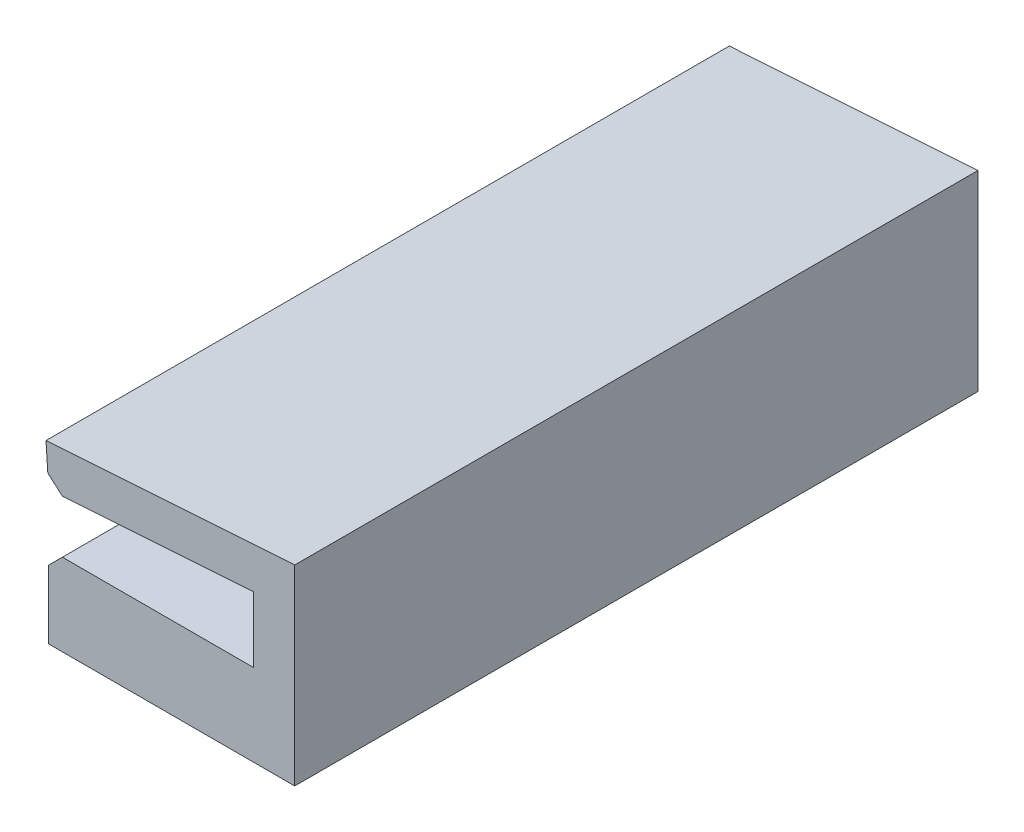
SolidWorks part; units mm, degrees
ref_plane "Plan de face" through (0, 0, 0) normal (0, 0, 1) x (1, 0, 0)
ref_plane "Plan de dessus" through (0, 0, 0) normal (0, 1, 0) x (1, 0, 0)
ref_plane "Plan de droite" through (0, 0, 0) normal (1, 0, 0) x (0, 0, -1)
sketch "Esquisse1" plane through (0, 0, 0) normal (0, 0, 1) x (1, 0, 0)
  line L1 (0, 4.8) -> (-6.0572, 4.8) construction
  line L9 (0, 4.8) -> (0, 0)
  line L10 (0, 0) -> (-15, 0)
  line L11 (3, -3) -> (-15, -3)
  line L12 (0, 4.8) -> (-15, 3.8)
  line L13 (3, 8.0067) -> (3, -3)
  line L14 (3, 8.0067) -> (-15.1996, 6.7934)
  line L15 (-15, 0) -> (-15, -3)
  line L16 (-15, 3.8) -> (-15.1996, 6.7934)
  line L17 (3.0665, 7.0089) -> (-15.133, 5.7956) construction
  dimension "D1" = 15
  dimension "D2" = 4.8
  dimension "D3" = 3.8
  dimension "D4" = 15
  dimension "D5" = 3
  dimension "D6" = 1
extrude "Boss.-Extru.1" add sketch "Esquisse1" along normal blind 50
sketch "Esquisse2" plane through (0, -3, 0) normal (0, -1, 0) x (1, 0, 0)
  line L0 (-6, 50) -> (-6, 0) construction
  line L1 (-15, 50) -> (3, 50) construction
  line L2 (-15, 0) -> (3, 0) construction
  line L3 (3, 25) -> (-15, 25) construction
  line L4 (3, 50) -> (3, 0) construction
  line L5 (-15, 50) -> (-15, 0) construction
  line L6 (-5.6368, 25) -> (-4.8424, 25.2712)
  line L7 (-15, 50) -> (3, 50)
  line L8 (-15, 50) -> (-15, 0)
  line L9 (-15, 0) -> (3, 0)
  line L10 (3, 50) -> (3, 0)
  line L11 (-5.6368, 25) -> (-4.8424, 24.7288)
  line L12 (-6.3632, 25) -> (-7.1576, 25.2712)
  line L13 (-6.3632, 25) -> (-7.1576, 24.7288)
  arc A2 (-4.8424, 25.2712) -> (-7.1576, 25.2712) centre (-6, 29.1) ccw
  arc A3 (-4.8424, 24.7288) -> (-7.1576, 24.7288) centre (-6, 20.9) cw
  arc A4 (-7.1576, 25.2712) -> (-6, 25.1) centre (-6, 29.1) ccw construction
  arc A5 (-6, 25.1) -> (-4.8424, 25.2712) centre (-6, 29.1) ccw construction
  arc A6 (-7.1576, 24.7288) -> (-6, 24.9) centre (-6, 20.9) cw construction
  arc A7 (-6, 24.9) -> (-4.8424, 24.7288) centre (-6, 20.9) cw construction
  dimension "D1" = 8
  dimension "D2" = 4.1
extrude "Boss.-Extru.2" add sketch "Esquisse2" along normal blind 3
chamfer "Chanfrein1" distance 1 angle 45 2 edges at (-15, 0, 25) (-15, 3.8, 25)
fillet "Congé1" radius 0.5 2 edges at (-6.3632, -4.5, 25) (-5.6368, -4.5, 25)
